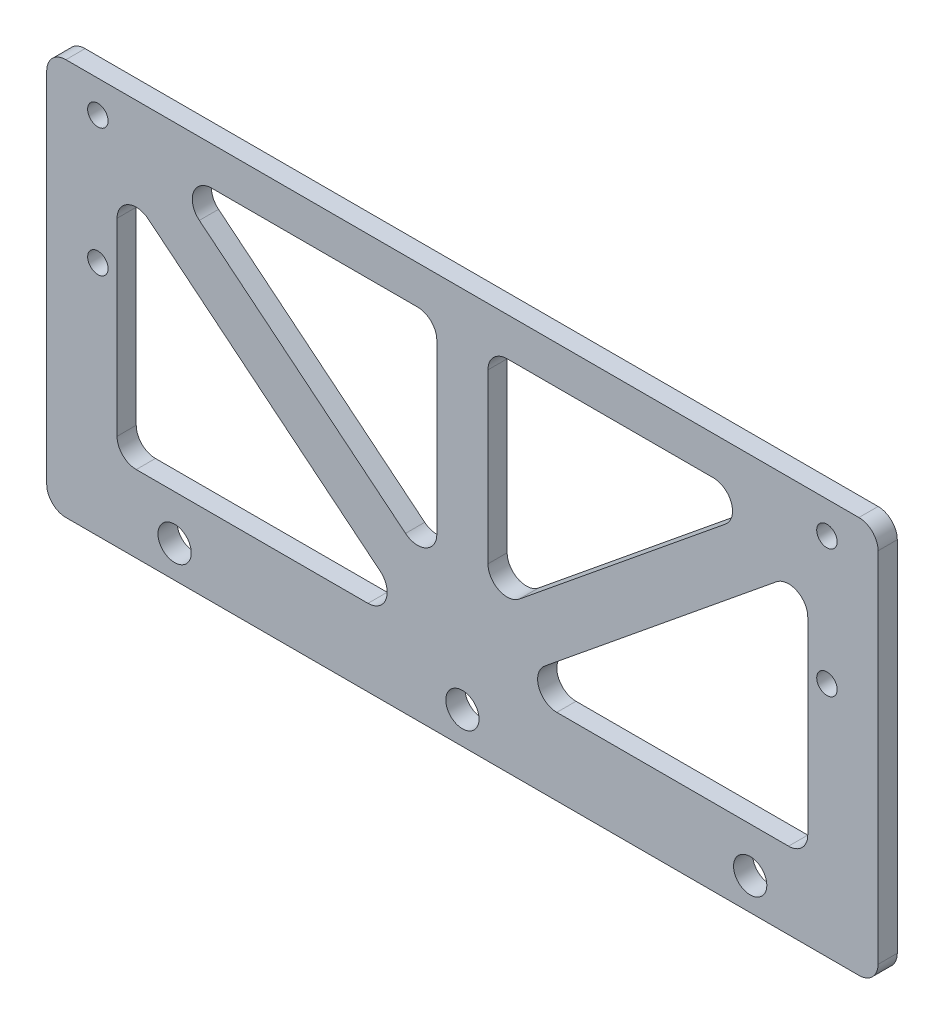
SolidWorks part; units mm, degrees
material "Thornel Mat VMA"
ref_plane "前视基准面" through (0, 0, 0) normal (0, 0, 1) x (1, 0, 0)
ref_plane "上视基准面" through (0, 0, 0) normal (0, 1, 0) x (1, 0, 0)
ref_plane "右视基准面" through (0, 0, 0) normal (1, 0, 0) x (0, 0, -1)
sketch "草图1" plane through (0, 0, 0) normal (0, 0, 1) x (1, 0, 0)
  line L1 (-65, 31) -> (65, 31)
  line L2 (-65, 31) -> (-65, -31)
  line L3 (-65, -31) -> (65, -31)
  line L4 (65, 31) -> (65, -31)
  line L5 (-65, 31) -> (65, -31) construction
  line L6 (-65, -31) -> (65, 31) construction
  point P0 (0, 0)
  dimension "D1" = 130
  dimension "D2" = 62
extrude "凸台-拉伸1" add sketch "草图1" along normal blind 3
sketch "草图2" plane through (0, 0, 3) normal (0, 0, 1) x (1, 0, 0)
  line L0 (-45, -26) -> (45, -26) construction
  line L1 (-65, -31) -> (65, -31) construction
  circle A0 centre (-45, -26) radius 2.6
  circle A1 centre (0, -26) radius 2.6
  circle A2 centre (45, -26) radius 2.6
  point P4 (0, -26)
  dimension "D3" = 5.2
  dimension "D1" = 5
  dimension "D2" = 90
extrude "切除-拉伸1" cut sketch "草图2" against normal through all
sketch "草图3" plane through (0, 0, 3) normal (0, 0, 1) x (1, 0, 0)
  line L0 (57, 26) -> (57, 6) construction
  line L1 (65, -31) -> (65, 31) construction
  line L2 (65, 31) -> (-65, 31) construction
  circle A0 centre (57, 26) radius 1.6
  circle A1 centre (57, 6) radius 1.6
  dimension "D4" = 3.2
  dimension "D1" = 20
  dimension "D2" = 8
  dimension "D3" = 5
extrude "切除-拉伸2" cut sketch "草图3" against normal through all
mirror "镜向1" about plane through (0, 0, 0) normal (1, 0, 0) of "切除-拉伸2"
sketch "草图4" plane through (0, 0, 3) normal (0, 0, 1) x (1, 0, 0)
  line L0 (-65, 31) -> (-65, -31) construction
  line L1 (-65, 31) -> (65, 31)
  line L2 (-65, 31) -> (-65, -31)
  line L3 (-65, -31) -> (65, -31)
  line L4 (65, 31) -> (65, -31)
  line L5 (-65, -31) -> (65, -31) construction
  line L6 (-54, 25) -> (0, -19)
  line L7 (-54, 25) -> (54, 25)
  line L8 (-54, 25) -> (-54, -19)
  line L9 (-54, -19) -> (54, -19)
  line L10 (54, 25) -> (54, -19)
  line L11 (0, -19) -> (54, 25)
  line L12 (0, 25) -> (0, -19)
  line L13 (-4, 25) -> (-4, -19)
  line L14 (-56.5267, 21.8991) -> (-2.5267, -22.1009)
  line L15 (2.5267, -22.1009) -> (56.5267, 21.8991)
  line L16 (4, 25) -> (4, -19)
  line L17 (-51.4733, 28.1009) -> (2.5267, -15.8991)
  line L18 (-2.5267, -15.8991) -> (51.4733, 28.1009)
  dimension "D1" = 11
  dimension "D2" = 11
  dimension "D3" = 6
  dimension "D4" = 12
  dimension "D5" = 4
  dimension "D6" = 4
extrude "切除-拉伸3" cut sketch "草图4" against normal through all contours L14 L8 L9 | L7 L17 L13 | L16 L18 L7 | L15 L9 L10
fillet "圆角1" radius 3 12 edges at (-4, 25, 1.5) (-4, -10.581, 1.5) (-47.6676, 25, 1.5) (47.6676, 25, 1.5) (4, -10.581, 1.5) (4, 25, 1.5) (-6.3324, -19, 1.5) (-54, 19.8403, 1.5) (54, 19.8403, 1.5) (6.3324, -19, 1.5) (54, -19, 1.5) (-54, -19, 1.5)
fillet "圆角2" radius 3 4 edges at (65, -31, 1.5) (-65, -31, 1.5) (65, 31, 1.5) (-65, 31, 1.5)
